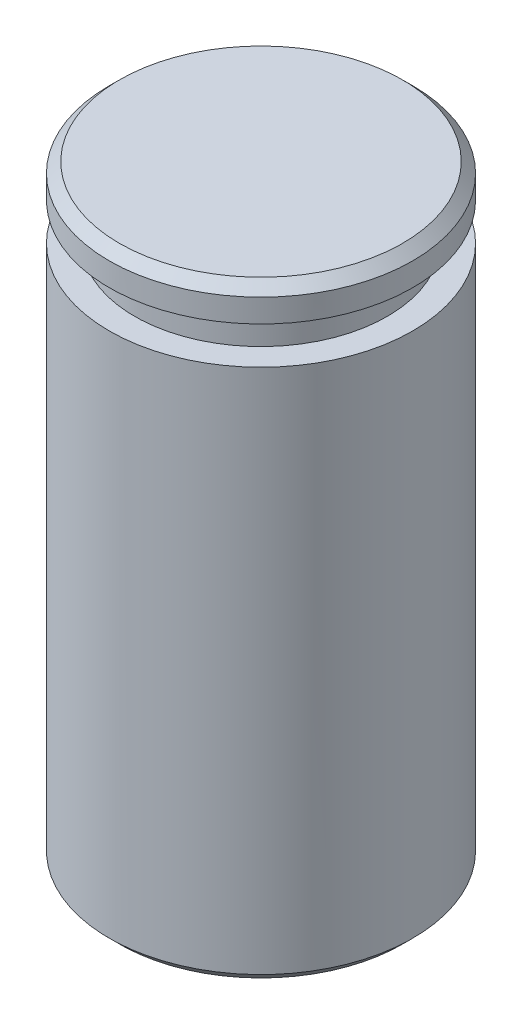
SolidWorks part; units mm, degrees
material "1060 Alloy"
ref_plane "Front Plane" through (0, 0, 0) normal (0, 0, 1) x (1, 0, 0)
ref_plane "Top Plane" through (0, 0, 0) normal (0, 1, 0) x (1, 0, 0)
ref_plane "Right Plane" through (0, 0, 0) normal (1, 0, 0) x (0, 0, -1)
sketch "Sketch1" plane through (0, 0, 0) normal (0, 0, 1) x (1, 0, 0)
  line L0 (0, 0) -> (0, 37.1759) construction
  line L2 (0, 0) -> (3, 0)
  line L3 (0, 0) -> (0, 12)
  line L4 (0, 12) -> (3, 12)
  line L5 (3, 0) -> (3, 12)
  dimension "D1" = 12
  dimension "D2" = 6
revolve "Revolve1" add sketch "Sketch1" angle 360 about L0
ref_plane "Plane1" through (0, 0, 0) normal (-1, 0, 0) x (0, 0, -1)
ref_plane "Plane2" through (0, 0, 0) normal (-1, 0, 0) x (0, 0, -1)
sketch "Sketch5" plane through (0, 0, 0) normal (-1, 0, 0) x (0, 0, -1)
  line L0 (4.55, -11.34) -> (2.5, -11.34)
  line L1 (4.55, -11.34) -> (4.55, -10.6)
  line L2 (4.55, -10.6) -> (2.5, -10.6)
  line L3 (2.5, -10.6) -> (2.5, -11.34)
  line L4 (0, -50.0288) -> (0, 49.9712) construction
  line L5 (3, 0) -> (-3, 0) construction
  dimension "D1" = 2.05
  dimension "D3" = 10.6
  dimension "D4" = 2.5
  dimension "D5" = 0.74
revolve "Groove for DIN 471 - 4 x 0.4, Circlip for shafts - normal1" cut sketch "Sketch5"
chamfer "Chanfrein1" distance 0.2 angle 45 2 edges at (0, 12, -3) (0, 0, -3)
